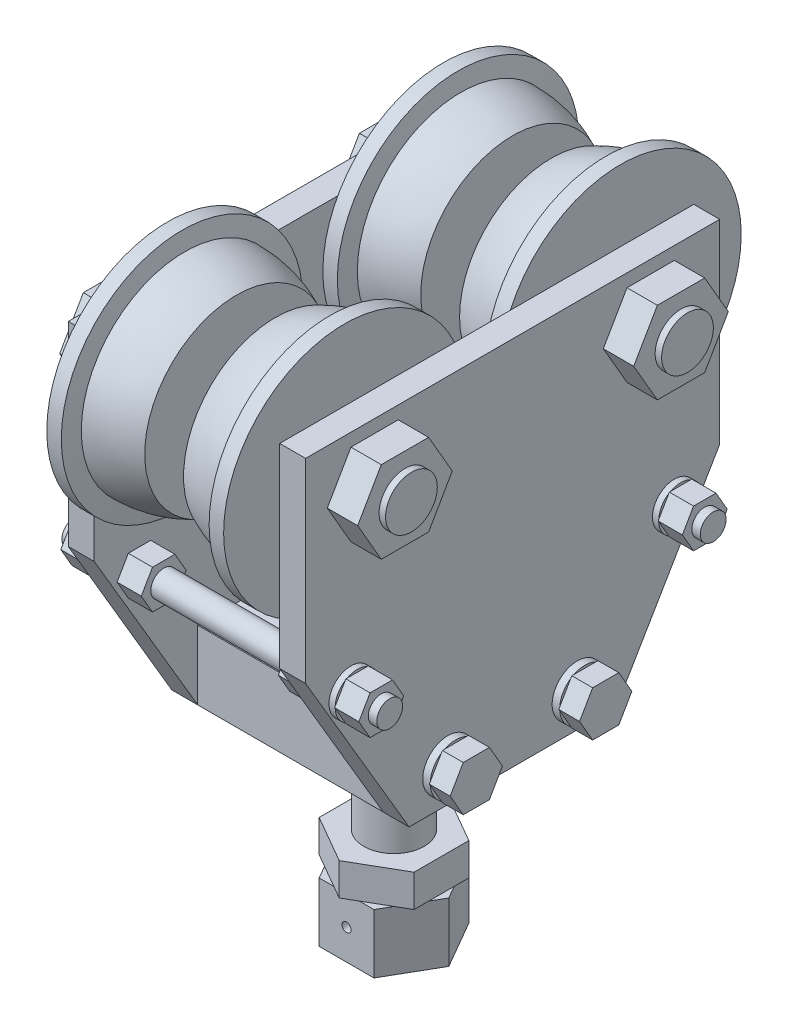
SolidWorks part; units mm, degrees
ref_plane "Front" through (0, 0, 0) normal (0, 0, 1) x (1, 0, 0)
ref_plane "Top" through (0, 0, 0) normal (0, 1, 0) x (1, 0, 0)
ref_plane "Right" through (0, 0, 0) normal (1, 0, 0) x (0, 0, -1)
ref_plane "Z PLANE" through (0, 0, 0) normal (0, 0, 1) x (1, 0, 0)
ref_plane "YOKE BOTTOM" through (0, 0, 0) normal (0, 1, 0) x (-1, 0, 0)
ref_plane "X PLANE" through (0, 0, 0) normal (1, 0, 0) x (0, 0, -1)
sketch "YOKE CROSS SECTION" plane through (0, 0, 0) normal (1, 0, 0) x (0, 0, -1)
  line L0 (0, 0) -> (0, 57.0916) construction
  line L1 (0, 84.8167) -> (0, -84.8167) construction
  line L2 (-76.2, 0) -> (76.2, 0)
  line L3 (69.1602, 0) -> (-69.1602, 0) construction
  line L4 (76.2, 0) -> (76.2, 50.8)
  line L5 (-76.2, 0) -> (-76.2, 50.8)
  line L6 (76.2, 50.8) -> (-76.2, 50.8)
  point P12 (0, 50.8)
  dimension "D1" = 50.8
  dimension "D2" = 152.4
ref_plane "1/2 YOKE LENGTH (A)" through (68.2625, 0, 0) normal (1, 0, 0) x (0, 0, -1)
ref_plane "WHEEL LOCATION" through (0, 0, 101.6) normal (0, 0, 1) x (1, 0, 0)
extrude "YOKE" add sketch "YOKE CROSS SECTION" along normal up to surface (68.2625 mm away) up to plane "1/2 YOKE LENGTH (A)"
sketch "SIDEPLATE PROFILE" plane through (68.2625, 0, 0) normal (1, 0, 0) x (0, 0, -1)
  line L0 (-152.4, 273.05) -> (152.4, 273.05)
  line L1 (0, 84.8167) -> (0, -84.8167) construction
  line L2 (152.4, 129.54) -> (76.2, 0)
  line L3 (-152.4, 129.54) -> (-76.2, 0)
  line L4 (0, 0) -> (-76.2, 0)
  line L5 (0, 0) -> (76.2, 0)
  line L6 (-152.4, 273.05) -> (-152.4, 129.54)
  line L7 (152.4, 129.54) -> (152.4, 273.05)
  line L8 (69.1602, 0) -> (-69.1602, 0) construction
  dimension "D1" = 76.2
  dimension "D2" = 76.2
  dimension "D3" = 76.2
  dimension "D4" = 76.2
  dimension "D5" = 129.54
  dimension "D6" = 143.51
  dimension "D7" = 129.54
ref_plane "WHEEL HEIGHT" through (0, 233.3625, 0) normal (0, 1, 0) x (-1, 0, 0)
ref_plane "YOKE SCREW LOCATION Z" through (0, 0, 47.625) normal (0, 0, 1) x (1, 0, 0)
ref_plane "YOKE SCREW LOCATION Y" through (0, 25.4, 0) normal (0, 1, 0) x (-1, 0, 0)
extrude "SIDEPLATE" add sketch "SIDEPLATE PROFILE" along normal blind 19.05
sketch "WHEEL PIN NUT PROFILE" plane through (87.3125, 0, 0) normal (1, 0, 0) x (0, 0, -1)
  line L0 (-101.6, 89.3799) -> (-101.6, -89.3799) construction
  line L1 (-66.7713, 233.3625) -> (-84.1857, 263.525)
  line L2 (-84.1857, 263.525) -> (-119.0143, 263.525)
  line L3 (-119.0143, 263.525) -> (-136.4287, 233.3625)
  line L4 (-136.4287, 233.3625) -> (-119.0143, 203.2)
  line L5 (-119.0143, 203.2) -> (-84.1857, 203.2)
  line L6 (-84.1857, 203.2) -> (-66.7713, 233.3625)
  line L7 (69.1602, 233.3625) -> (-69.1602, 233.3625) construction
  circle A0 centre (-101.6, 233.3625) radius 13.4938 construction
  dimension "D1" = 60.325
extrude "WHEEL PIN NUT" add sketch "WHEEL PIN NUT PROFILE" along normal blind 22.352
sketch "WHEEL PIN PROJECTION PROFILE" plane through (109.6645, 0, 0) normal (1, 0, 0) x (0, 0, -1)
  line L0 (-101.6, 89.3799) -> (-101.6, -89.3799) construction
  line L3 (69.1602, 233.3625) -> (-69.1602, 233.3625) construction
  circle A0 centre (-101.6, 233.3625) radius 19.05
  dimension "D1" = 38.1
extrude "WHEEL PIN PROJECTION" add sketch "WHEEL PIN PROJECTION PROFILE" along normal blind 4.7625
sketch "LOCKNUTS PROFILE" plane through (87.3125, 0, 0) normal (1, 0, 0) x (0, 0, -1)
  line L0 (-47.625, 84.8167) -> (-47.625, -84.8167) construction
  line L1 (50, 25.4) -> (-50, 25.4) construction
  circle A0 centre (-47.625, 25.4) radius 18.542
  dimension "D1" = 37.084
extrude "LOCKNUTS" add sketch "LOCKNUTS PROFILE" along normal blind 5.5626
sketch "SCREWS PROFILE" plane through (92.8751, 0, 0) normal (1, 0, 0) x (0, 0, -1)
  line L0 (50, 25.4) -> (-50, 25.4) construction
  line L1 (-28.3776, 25.4) -> (-38.0013, 42.0688)
  line L2 (-38.0013, 42.0688) -> (-57.2487, 42.0688)
  line L3 (-57.2487, 42.0688) -> (-66.8724, 25.4)
  line L4 (-66.8724, 25.4) -> (-57.2487, 8.7313)
  line L5 (-57.2487, 8.7313) -> (-38.0013, 8.7313)
  line L6 (-38.0013, 8.7313) -> (-28.3776, 25.4)
  line L7 (-47.625, 84.8167) -> (-47.625, -84.8167) construction
  circle A0 centre (-47.625, 25.4) radius 16.6687 construction
  dimension "D1" = 33.3375
extrude "SCREWS" add sketch "SCREWS PROFILE" along normal blind 15.3416
sketch "PROFILE" plane through (0, 50.8, 0) normal (0, 1, 0) x (-1, 0, 0)
  line L0 (84.8167, 0) -> (-84.8167, 0) construction
  line L1 (0, 83.2389) -> (0, -83.2389) construction
  circle A0 centre (0, 0) radius 30.1625
  dimension "D1" = 60.325
extrude "KING BOLT HEAD" add sketch "PROFILE" along normal blind 38.1
mirror "Mirror1" about plane through (0, 0, 0) normal (0, 0, 1) of "WHEEL PIN PROJECTION", "WHEEL PIN NUT"
mirror "Mirror YOKE SCREWS" about plane through (0, 0, 0) normal (0, 0, 1) of "SCREWS", "LOCKNUTS"
mirror "Mirror SIDE 1" about plane through (0, 0, 0) normal (1, 0, 0) of bodies 112
ref_plane "TOP OF NUT" through (0, -83.0521, 0) normal (0, 1, 0) x (-1, 0, 0)
sketch "DIA." plane through (0, 0, 0) normal (0, -1, 0) x (1, 0, 0)
  line L0 (84.8167, 0) -> (-84.8167, 0) construction
  line L1 (0, -83.2389) -> (0, 83.2389) construction
  circle A0 centre (0, 0) radius 22.225
  dimension "D1" = 44.45
extrude "KING BOLT" add sketch "DIA." along normal up to surface (83.0521 mm away) up to plane "TOP OF NUT"
sketch "KING BOLT JAN NUT PROFILE" plane through (0, -83.0521, 0) normal (0, -1, 0) x (1, 0, 0)
  line L0 (84.8167, 0) -> (-84.8167, 0) construction
  line L1 (0, -40.3279) -> (34.925, -20.164)
  line L2 (34.925, -20.164) -> (34.925, 20.164)
  line L3 (34.925, 20.164) -> (0, 40.3279)
  line L4 (0, 40.3279) -> (-34.925, 20.164)
  line L5 (-34.925, 20.164) -> (-34.925, -20.164)
  line L6 (-34.925, -20.164) -> (0, -40.3279)
  line L7 (0, -83.2389) -> (0, 83.2389) construction
  circle A0 centre (0, 0) radius 34.925 construction
  dimension "D1" = 69.85
extrude "KING BOLT JAM NUT" add sketch "KING BOLT JAN NUT PROFILE" along normal blind 23.8125
sketch "KING BOLT NUT PROFILE" plane through (0, -106.8646, 0) normal (0, -1, 0) x (1, 0, 0)
  line L1 (40.3279, 0) -> (20.164, 34.925)
  line L2 (20.164, 34.925) -> (-20.164, 34.925)
  line L3 (-20.164, 34.925) -> (-40.3279, 0)
  line L4 (-40.3279, 0) -> (-20.164, -34.925)
  line L5 (-20.164, -34.925) -> (20.164, -34.925)
  line L6 (20.164, -34.925) -> (40.3279, 0)
  line L10 (0, -83.2389) -> (0, 83.2389) construction
  line L11 (84.8167, 0) -> (-84.8167, 0) construction
  circle A0 centre (0, 0) radius 34.925 construction
  dimension "D1" = 69.85
extrude "KING BOLT NUT" add sketch "KING BOLT NUT PROFILE" along normal blind 43.6372
sketch "Sketch5" plane through (0, -150.5018, 0) normal (0, -1, 0) x (1, 0, 0)
  circle A0 centre (0, 0) radius 22.225 construction
  circle A1 centre (0, 0) radius 22.225
extrude "EXTENDED KING BOLT" add sketch "Sketch5" along normal blind 9.525
chamfer "Chamfer1" distance 2.3812 angle 45 1 edges at (0, -160.0268, -22.225)
ref_plane "MOUNTING REF PLANE" through (0, -34.925, 0) normal (0, 1, 0) x (-1, 0, 0)
ref_plane "THREADED ROD LOCATION" through (0, 0, 119.0625) normal (0, 0, 1) x (1, 0, 0)
ref_plane "THREADED ROD HEIGHT" through (0, 107.95, 0) normal (0, 1, 0) x (-1, 0, 0)
sketch "Sketch6" plane through (68.2625, 0, 0) normal (1, 0, 0) x (0, 0, -1)
  line L0 (69.1602, 107.95) -> (-69.1602, 107.95) construction
  line L1 (-119.0625, 84.8167) -> (-119.0625, -84.8167) construction
  circle A0 centre (-119.0625, 107.95) radius 9.525
  dimension "D1" = 19.05
extrude "THREADED ROD" add sketch "Sketch6" along normal blind 47.625 and the other way up to surface (68.2625 mm away) other way up to plane "X PLANE"
sketch "Sketch7" plane through (68.2625, 0, 0) normal (1, 0, 0) x (0, 0, -1)
  line L0 (69.1602, 107.95) -> (-69.1602, 107.95) construction
  line L1 (-102.5647, 107.95) -> (-110.8136, 122.2375)
  line L2 (-110.8136, 122.2375) -> (-127.3114, 122.2375)
  line L3 (-127.3114, 122.2375) -> (-135.5603, 107.95)
  line L4 (-135.5603, 107.95) -> (-127.3114, 93.6625)
  line L5 (-127.3114, 93.6625) -> (-110.8136, 93.6625)
  line L6 (-110.8136, 93.6625) -> (-102.5647, 107.95)
  line L7 (-119.0625, 84.8167) -> (-119.0625, -84.8167) construction
  circle A0 centre (-119.0625, 107.95) radius 14.2875 construction
  dimension "D1" = 28.575
extrude "THREADED ROD NUTS INNER " add sketch "Sketch7" against normal blind 17.8054
sketch "Sketch8" plane through (87.3125, 0, 0) normal (1, 0, 0) x (0, 0, -1)
  line L0 (69.1602, 107.95) -> (-69.1602, 107.95) construction
  line L1 (-119.0625, 84.8167) -> (-119.0625, -84.8167) construction
  circle A0 centre (-119.0625, 107.95) radius 16.129
  dimension "D1" = 32.258
extrude "THREADED ROD LOCKWASHER " add sketch "Sketch8" along normal blind 4.572
sketch "Sketch9" plane through (91.8845, 0, 0) normal (1, 0, 0) x (0, 0, -1)
  line L0 (-102.5647, 107.95) -> (-110.8136, 122.2375) construction
  line L1 (-110.8136, 93.6625) -> (-102.5647, 107.95) construction
  line L2 (-127.3114, 93.6625) -> (-110.8136, 93.6625) construction
  line L3 (-135.5603, 107.95) -> (-127.3114, 93.6625) construction
  line L4 (-127.3114, 122.2375) -> (-135.5603, 107.95) construction
  line L5 (-110.8136, 122.2375) -> (-127.3114, 122.2375) construction
  line L6 (-102.5647, 107.95) -> (-110.8136, 122.2375)
  line L7 (-110.8136, 93.6625) -> (-102.5647, 107.95)
  line L8 (-127.3114, 93.6625) -> (-110.8136, 93.6625)
  line L9 (-135.5603, 107.95) -> (-127.3114, 93.6625)
  line L10 (-127.3114, 122.2375) -> (-135.5603, 107.95)
  line L11 (-110.8136, 122.2375) -> (-127.3114, 122.2375)
extrude "THREADED ROD NUT OUTER" add sketch "Sketch9" along normal blind 17.8054
mirror "Mirror2" about plane through (0, 0, 0) normal (0, 0, 1) of "THREADED ROD NUT OUTER", "THREADED ROD LOCKWASHER ", "THREADED ROD NUTS INNER ", "THREADED ROD"
mirror "Mirror3" about plane through (0, 0, 0) normal (1, 0, 0) of "Mirror2", "THREADED ROD", "THREADED ROD NUTS INNER ", "THREADED ROD LOCKWASHER ", "THREADED ROD NUT OUTER"
sketch "Sketch10" plane through (0, 0, 34.925) normal (0, 0, 1) x (1, 0, 0)
  line L0 (0, -83.2389) -> (0, 83.2389) construction
  line L1 (-20.164, -150.5018) -> (-40.3279, -150.5018) construction
  circle A0 centre (0, -128.2768) radius 3.3655
  dimension "D1" = 6.731
  dimension "D2" = 22.225
extrude "COTTER PIN HOLE" cut sketch "Sketch10" against normal through all
sketch "Sketch11" plane through (0, 0, 101.6) normal (0, 0, 1) x (1, 0, 0)
  line L0 (68.2625, 233.3625) -> (14.2875, 233.3625)
  line L1 (14.2875, 233.3625) -> (14.2875, 300.9844)
  line L2 (68.2625, 260.35) -> (68.2625, 233.3625)
  line L3 (65.0875, 260.35) -> (65.0875, 322.2625)
  line L4 (65.0875, 260.35) -> (68.2625, 260.35)
  line L5 (65.0875, 322.2625) -> (54.399, 322.2625)
  line L6 (52.3875, 309.5625) -> (54.399, 322.2625)
  line L7 (69.1602, 233.3625) -> (-69.1602, 233.3625) construction
  line L8 (68.2625, -75.0522) -> (68.2625, 75.0522) construction
  arc A0 (52.3875, 309.5625) -> (14.2875, 300.9844) centre (52.3875, 220.6625) ccw
  dimension "D5" = 88.9
  dimension "D1" = 53.975
  dimension "D2" = 3.175
  dimension "D3" = 13.8635
  dimension "D4" = 15.875
  dimension "D6" = 67.6219
  dimension "D7" = 76.2
  dimension "D8" = 88.9
  dimension "D9" = 26.9875
revolve "WHEEL" add sketch "Sketch11" angle 360 about axis through (114.427, 233.3625, 101.6) along (-1, 0, 0)
mirror "Mirror4" about plane through (0, 0, 0) normal (0, 0, 1) of "WHEEL"
mirror "Mirror5" about plane through (0, 0, 0) normal (1, 0, 0) of "Mirror4", "WHEEL"
sketch "Sketch12" plane through (0, 0, 0) normal (0, -1, 0) x (1, 0, 0)
  circle A0 centre (0, 0) radius 25.4
  circle A1 centre (0, 0) radius 30.1663
  dimension "D1" = 50.8
  dimension "D2" = 60.3326
extrude "SPACER" [suppressed] add sketch "Sketch12" along normal blind 12.7
ref_plane "TREAD OF TRACK" through (0, 157.1625, 0) normal (0, 1, 0) x (-1, 0, 0)
